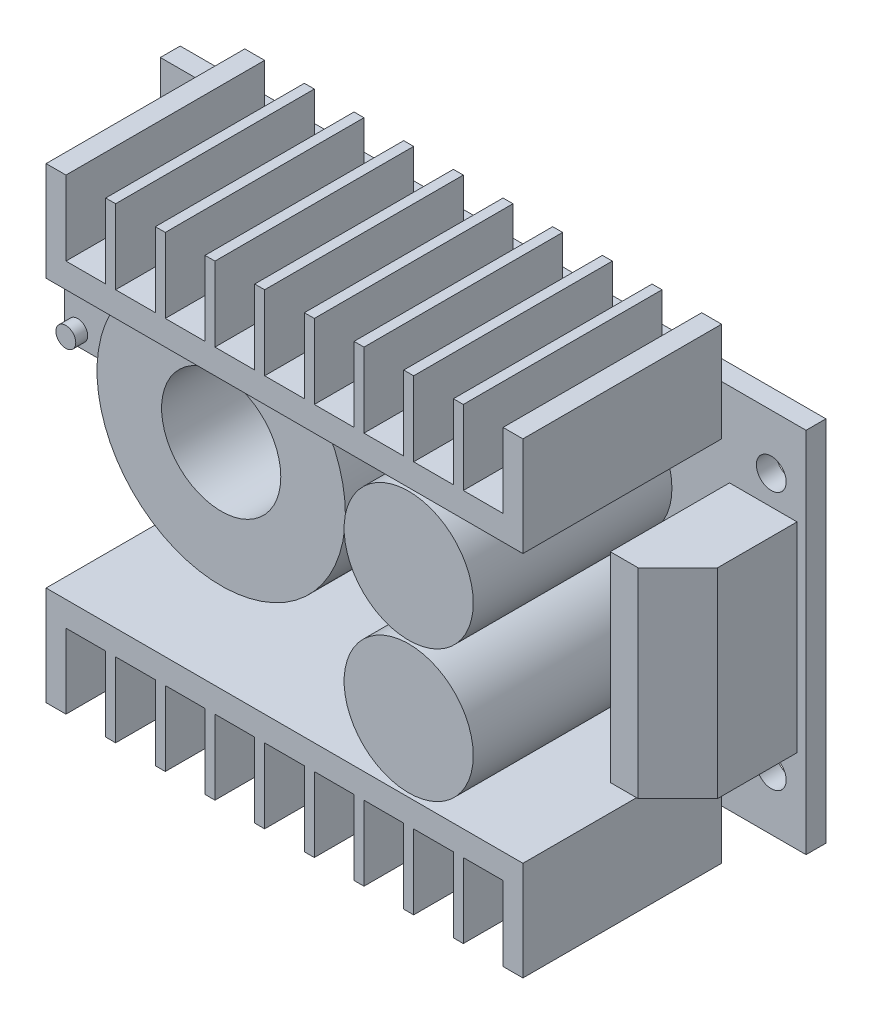
SolidWorks part; units mm, degrees
ref_plane "Front" through (0, 0, 0) normal (0, 0, 1) x (1, 0, 0)
ref_plane "Top" through (0, 0, 0) normal (0, 1, 0) x (1, 0, 0)
ref_plane "Right" through (0, 0, 0) normal (1, 0, 0) x (0, 0, -1)
sketch "Эскиз1" plane through (0, 0, 0) normal (0, 0, 1) x (1, 0, 0)
  line L1 (-32.5, 18.5) -> (32.5, 18.5)
  line L2 (-32.5, 18.5) -> (-32.5, -18.5)
  line L3 (-32.5, -18.5) -> (32.5, -18.5)
  line L4 (32.5, 18.5) -> (32.5, -18.5)
  line L5 (0, -18.5) -> (0, 18.5) construction
  line L6 (-32.5, 0) -> (32.5, 0) construction
  point P0 (0, 0)
  dimension "D1" = 37
  dimension "D2" = 65
extrude "Бобышка-Вытянуть1" add sketch "Эскиз1" along normal blind 2
sketch "Эскиз2" plane through (0, 0, 2) normal (0, 0, 1) x (1, 0, 0)
  line L0 (32.5, 18.5) -> (-32.5, 18.5) construction
  line L1 (-24, 23.5) -> (24, 23.5) construction
  line L2 (-24, 23.5) -> (-24, 13.5)
  line L3 (-24, 13.5) -> (24, 13.5)
  line L4 (24, 23.5) -> (24, 13.5)
  line L5 (0, 13.5) -> (0, 23.5) construction
  line L6 (-24, 18.5) -> (24, 18.5) construction
  line L7 (-22, 23.5) -> (-24, 23.5)
  line L8 (-2, 16) -> (2, 16)
  line L9 (-2, 16) -> (-2, 23.5)
  line L11 (2, 16) -> (2, 23.5)
  line L12 (0, 23.5) -> (0, 16) construction
  line L13 (-2, 19.75) -> (2, 19.75) construction
  line L14 (-3, 23.5) -> (-2, 23.5)
  line L15 (-3, 16) -> (-3, 23.5)
  line L16 (-7, 16) -> (-3, 16)
  line L17 (-7, 16) -> (-7, 23.5)
  line L18 (-8, 23.5) -> (-7, 23.5)
  line L19 (-8, 16) -> (-8, 23.5)
  line L20 (-12, 16) -> (-8, 16)
  line L21 (-12, 16) -> (-12, 23.5)
  line L22 (-13, 23.5) -> (-12, 23.5)
  line L23 (-13, 16) -> (-13, 23.5)
  line L24 (-17, 16) -> (-13, 16)
  line L25 (-17, 16) -> (-17, 23.5)
  line L26 (-18, 23.5) -> (-17, 23.5)
  line L27 (-18, 16) -> (-18, 23.5)
  line L28 (-22, 16) -> (-18, 16)
  line L29 (-22, 16) -> (-22, 23.5)
  line L30 (2, 23.5) -> (3, 23.5)
  line L31 (3, 16) -> (3, 23.5)
  line L32 (3, 16) -> (7, 16)
  line L33 (7, 16) -> (7, 23.5)
  line L34 (7, 23.5) -> (8, 23.5)
  line L35 (8, 16) -> (8, 23.5)
  line L36 (8, 16) -> (12, 16)
  line L37 (12, 16) -> (12, 23.5)
  line L38 (12, 23.5) -> (13, 23.5)
  line L39 (13, 16) -> (13, 23.5)
  line L40 (13, 16) -> (17, 16)
  line L41 (17, 16) -> (17, 23.5)
  line L42 (17, 23.5) -> (18, 23.5)
  line L43 (18, 16) -> (18, 23.5)
  line L44 (18, 16) -> (22, 16)
  line L45 (22, 16) -> (22, 23.5)
  line L46 (22, 23.5) -> (24, 23.5)
  line L47 (-32.5, 0) -> (32.5, 0) construction
  line L48 (-32.5, 18.5) -> (-32.5, -18.5) construction
  line L49 (32.5, -18.5) -> (32.5, 18.5) construction
  line L50 (-2, -19.75) -> (2, -19.75) construction
  line L51 (0, -23.5) -> (0, -16) construction
  line L52 (-24, -18.5) -> (24, -18.5) construction
  line L53 (0, -13.5) -> (0, -23.5) construction
  line L54 (-24, -23.5) -> (24, -23.5) construction
  line L55 (22, -23.5) -> (24, -23.5)
  line L56 (22, -16) -> (22, -23.5)
  line L57 (18, -16) -> (22, -16)
  line L58 (18, -16) -> (18, -23.5)
  line L59 (17, -23.5) -> (18, -23.5)
  line L60 (17, -16) -> (17, -23.5)
  line L61 (13, -16) -> (17, -16)
  line L62 (13, -16) -> (13, -23.5)
  line L63 (12, -23.5) -> (13, -23.5)
  line L64 (12, -16) -> (12, -23.5)
  line L65 (8, -16) -> (12, -16)
  line L66 (8, -16) -> (8, -23.5)
  line L67 (7, -23.5) -> (8, -23.5)
  line L68 (7, -16) -> (7, -23.5)
  line L69 (3, -16) -> (7, -16)
  line L70 (3, -16) -> (3, -23.5)
  line L71 (2, -23.5) -> (3, -23.5)
  line L72 (-22, -16) -> (-22, -23.5)
  line L73 (-22, -16) -> (-18, -16)
  line L74 (-18, -16) -> (-18, -23.5)
  line L75 (-18, -23.5) -> (-17, -23.5)
  line L76 (-17, -16) -> (-17, -23.5)
  line L77 (-17, -16) -> (-13, -16)
  line L78 (-13, -16) -> (-13, -23.5)
  line L79 (-13, -23.5) -> (-12, -23.5)
  line L80 (-12, -16) -> (-12, -23.5)
  line L81 (-12, -16) -> (-8, -16)
  line L82 (-8, -16) -> (-8, -23.5)
  line L83 (-8, -23.5) -> (-7, -23.5)
  line L84 (-7, -16) -> (-7, -23.5)
  line L85 (-7, -16) -> (-3, -16)
  line L86 (-3, -16) -> (-3, -23.5)
  line L87 (-3, -23.5) -> (-2, -23.5)
  line L88 (2, -16) -> (2, -23.5)
  line L89 (-2, -16) -> (-2, -23.5)
  line L90 (-2, -16) -> (2, -16)
  line L91 (-22, -23.5) -> (-24, -23.5)
  line L92 (24, -23.5) -> (24, -13.5)
  line L93 (-24, -13.5) -> (24, -13.5)
  line L94 (-24, -23.5) -> (-24, -13.5)
  point P0 (0, 18.5)
  point P6 (0, 19.75)
  point P103 (0, -19.75)
  point P104 (0, -18.5)
  dimension "D1" = 10
  dimension "D2" = 48
  dimension "D3" = 7.5
  dimension "D4" = 4
  dimension "D5" = 5
  dimension "D6" = 5
extrude "Бобышка-Вытянуть2" add sketch "Эскиз2" along normal blind 20
sketch "Эскиз3" plane through (0, 0, 2) normal (0, 0, 1) x (1, 0, 0)
  line L0 (12.5, 23.5) -> (12.5, -23.5) construction
  line L1 (13, 23.5) -> (12, 23.5) construction
  line L2 (12, -23.5) -> (13, -23.5) construction
  circle A0 centre (12.5, 6.6916) radius 6.5
  circle A1 centre (12.5, -6.6124) radius 6.5
  dimension "D1" = 13
  dimension "D2" = 13
extrude "Бобышка-Вытянуть3" add sketch "Эскиз3" along normal blind 20
sketch "Эскиз4" plane through (0, 0, 2) normal (0, 0, 1) x (1, 0, 0)
  circle A0 centre (-14.3735, 0) radius 12.5
  circle A1 centre (-14.3735, 0) radius 6
  dimension "D1" = 25
  dimension "D2" = 12
extrude "Бобышка-Вытянуть4" add sketch "Эскиз4" along normal blind 12
sketch "Эскиз5" plane through (0, 0, 2) normal (0, 0, 1) x (1, 0, 0)
  line L1 (-32.1494, 9.1427) -> (-27.1494, 9.1427)
  line L2 (-32.1494, 9.1427) -> (-32.1494, -0.8573)
  line L3 (-32.1494, -0.8573) -> (-27.1494, -0.8573)
  line L4 (-27.1494, 9.1427) -> (-27.1494, -0.8573)
  line L5 (-29.6494, -0.8573) -> (-29.6494, 9.1427) construction
  line L6 (-32.1494, 4.1427) -> (-27.1494, 4.1427) construction
  point P0 (-29.6494, 4.1427)
  dimension "D1" = 10
  dimension "D2" = 5
extrude "Бобышка-Вытянуть5" add sketch "Эскиз5" along normal blind 10
sketch "Эскиз6" plane through (0, 0, 12) normal (0, 0, 1) x (1, 0, 0)
  circle A0 centre (-30.8135, 0.582) radius 1
  dimension "D1" = 2
extrude "Бобышка-Вытянуть6" add sketch "Эскиз6" along normal blind 1.2
sketch "Эскиз7" plane through (0, 0, 2) normal (0, 0, 1) x (1, 0, 0)
  line L1 (24.796, 10.0615) -> (31.5947, 10.0615)
  line L2 (24.796, 10.0615) -> (24.796, -10.0615)
  line L3 (24.796, -10.0615) -> (31.5947, -10.0615)
  line L4 (31.5947, 10.0615) -> (31.5947, -10.0615)
  line L5 (28.1954, -10.0615) -> (28.1954, 10.0615) construction
  line L6 (24.796, 0) -> (31.5947, 0) construction
  point P0 (28.1954, 0)
  dimension "D1" = 20.1231
  dimension "D2" = 6.7987
extrude "Бобышка-Вытянуть7" add sketch "Эскиз7" along normal blind 12
chamfer "Фаска1" distance 4 angle 45 1 edges at (31.5947, 0, 14)
sketch "Эскиз8" plane through (0, 0, 2) normal (0, 0, 1) x (1, 0, 0)
  line L1 (-29, 13) -> (29, 13) construction
  line L2 (-29, 13) -> (-29, -13) construction
  line L3 (-29, -13) -> (29, -13) construction
  line L4 (29, 13) -> (29, -13) construction
  line L5 (0, -13) -> (0, 13) construction
  line L6 (-29, 0) -> (29, 0) construction
  circle A0 centre (-29, 13) radius 1.5
  circle A1 centre (29, 13) radius 1.5
  circle A2 centre (29, -13) radius 1.5
  circle A3 centre (-29, -13) radius 1.5
  point P0 (0, 0)
  dimension "D3" = 3
  dimension "D4" = 3
  dimension "D5" = 3
  dimension "D6" = 3
  dimension "D1" = 26
  dimension "D2" = 58
extrude "Вырез-Вытянуть1" cut sketch "Эскиз8" against normal through all
